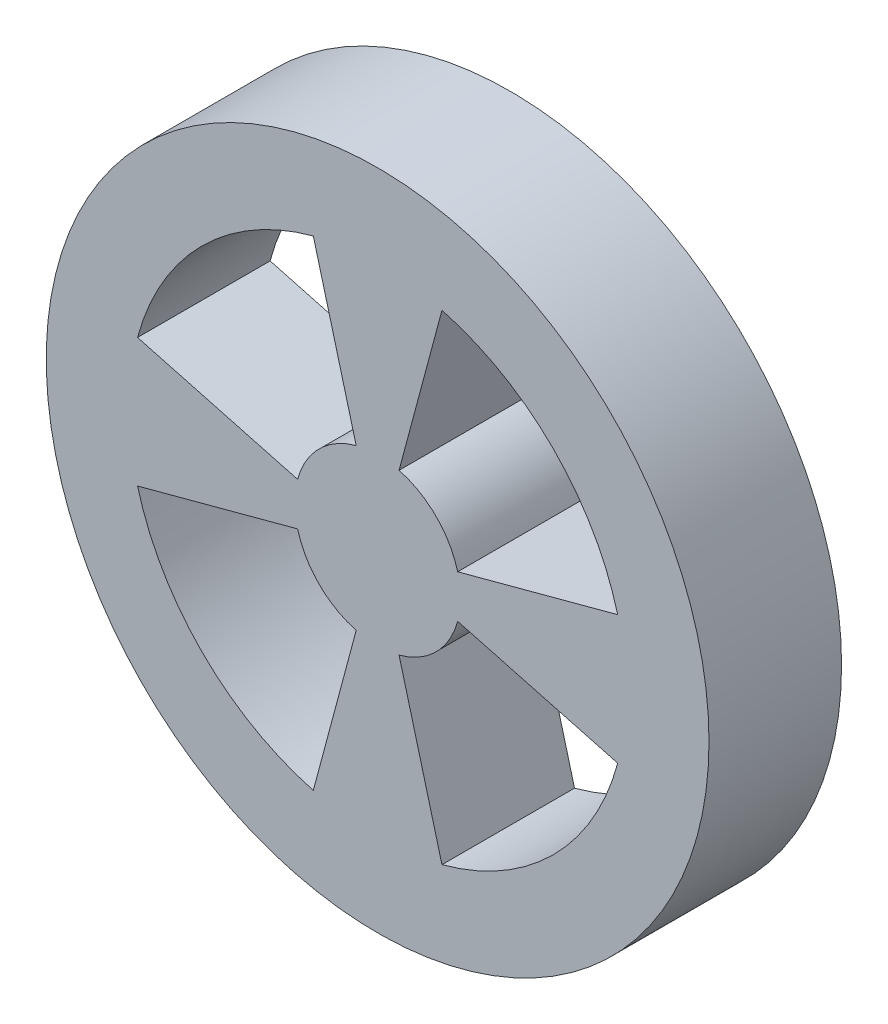
SolidWorks part; units mm, degrees
ref_plane "Front Plane" through (0, 0, 0) normal (0, 0, 1) x (1, 0, 0)
ref_plane "Top Plane" through (0, 0, 0) normal (0, 1, 0) x (1, 0, 0)
ref_plane "Right Plane" through (0, 0, 0) normal (1, 0, 0) x (0, 0, -1)
sketch "Sketch1" plane through (0, 0, 0) normal (0, 0, 1) x (1, 0, 0)
  line L0 (-0.2272, 0) -> (0.3326, 0) construction
  line L1 (0, 0.3879) -> (0, -0.3726) construction
  line L2 (-0.7244, 0.1941) -> (-0.2415, 0.0647)
  line L3 (-0.1941, 0.7244) -> (-0.0647, 0.2415)
  line L4 (0.1941, 0.7244) -> (0.0647, 0.2415)
  line L5 (0.7244, 0.1941) -> (0.2415, 0.0647)
  line L6 (0.1941, -0.7244) -> (0.0647, -0.2415)
  line L7 (0.7244, -0.1941) -> (0.2415, -0.0647)
  line L8 (-0.1941, -0.7244) -> (-0.0647, -0.2415)
  line L9 (-0.7244, -0.1941) -> (-0.2415, -0.0647)
  circle A0 centre (0, 0) radius 1
  arc A3 (-0.1941, 0.7244) -> (-0.7244, 0.1941) centre (0, 0) ccw
  arc A4 (-0.0647, 0.2415) -> (-0.2415, 0.0647) centre (0, 0) ccw
  circle A5 centre (0, 0) radius 0.25 construction
  circle A6 centre (0, 0) radius 0.75 construction
  arc A7 (0.1941, 0.7244) -> (0.7244, 0.1941) centre (0, 0) cw
  arc A8 (0.0647, 0.2415) -> (0.2415, 0.0647) centre (0, 0) cw
  arc A9 (0.0647, -0.2415) -> (0.2415, -0.0647) centre (0, 0) ccw
  arc A10 (0.1941, -0.7244) -> (0.7244, -0.1941) centre (0, 0) ccw
  arc A11 (-0.1941, -0.7244) -> (-0.7244, -0.1941) centre (0, 0) cw
  arc A12 (-0.0647, -0.2415) -> (-0.2415, -0.0647) centre (0, 0) cw
  dimension "D1" = 2
  dimension "D2" = 0.5
  dimension "D3" = 1.5
  dimension "D4" = 15
  dimension "D5" = 15
extrude "Boss-Extrude1" add sketch "Sketch1" along normal blind 0.4
